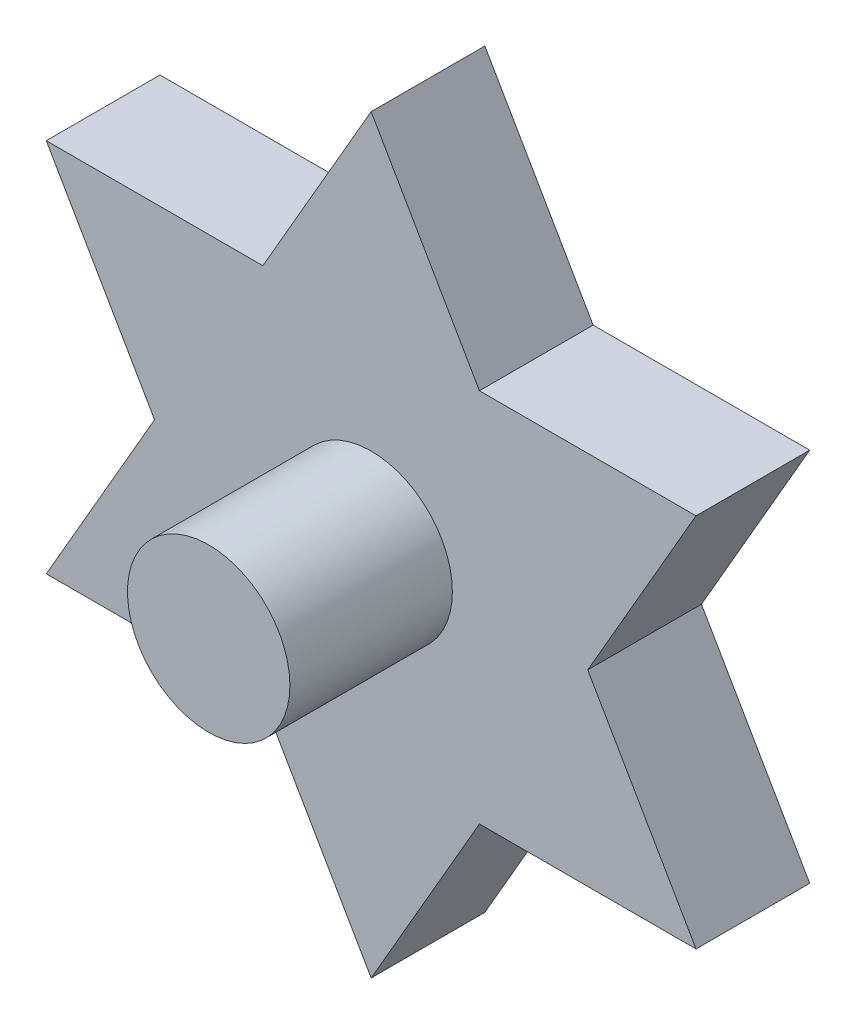
SolidWorks part; units mm, degrees
ref_plane "Plan de face" through (0, 0, 0) normal (0, 0, 1) x (1, 0, 0)
ref_plane "Plan de dessus" through (0, 0, 0) normal (0, 1, 0) x (1, 0, 0)
ref_plane "Plan de droite" through (0, 0, 0) normal (1, 0, 0) x (0, 0, -1)
sketch "Esquisse1" plane through (0, 0, 0) normal (0, 0, 1) x (1, 0, 0)
  line L0 (-20, -11.547) -> (0, 23.094) construction
  line L1 (0, 23.094) -> (20, -11.547) construction
  line L2 (20, -11.547) -> (-20, -11.547) construction
  line L3 (0, -23.094) -> (-20, 11.547) construction
  line L4 (-20, 11.547) -> (20, 11.547) construction
  line L5 (20, 11.547) -> (0, -23.094) construction
  line L6 (0, -23.094) -> (0, 23.094) construction
  line L7 (-20, 11.547) -> (20, -11.547) construction
  line L8 (-20, 11.547) -> (-6.6667, 11.547)
  line L9 (-6.6667, 11.547) -> (0, 23.094)
  line L10 (0, 23.094) -> (6.6667, 11.547)
  line L11 (6.6667, 11.547) -> (20, 11.547)
  line L12 (20, 11.547) -> (13.3333, 0)
  line L13 (13.3333, 0) -> (20, -11.547)
  line L14 (20, -11.547) -> (6.6667, -11.547)
  line L15 (6.6667, -11.547) -> (0, -23.094)
  line L16 (0, -23.094) -> (-6.6667, -11.547)
  line L17 (-6.6667, -11.547) -> (-20, -11.547)
  line L18 (-20, -11.547) -> (-13.3333, 0)
  line L19 (-13.3333, 0) -> (-20, 11.547)
  dimension "D1" = 40
extrude "Boss.-Extru.1" add sketch "Esquisse1" along normal blind 7
sketch "Esquisse2" plane through (0, 0, 7) normal (0, 0, 1) x (1, 0, 0)
  circle A0 centre (0, 0) radius 5
  dimension "D1" = 10
extrude "Boss.-Extru.2" add sketch "Esquisse2" along normal blind 10
